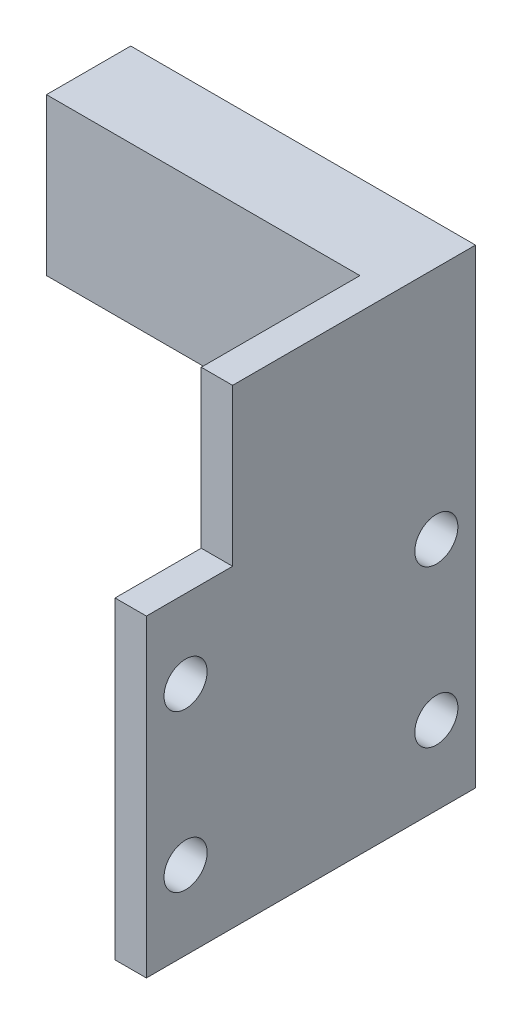
SolidWorks part; units mm, degrees
ref_plane "Front Plane" through (0, 0, 0) normal (0, 0, 1) x (1, 0, 0)
ref_plane "Top Plane" through (0, 0, 0) normal (0, 1, 0) x (1, 0, 0)
ref_plane "Right Plane" through (0, 0, 0) normal (1, 0, 0) x (0, 0, -1)
sketch "Sketch1" plane through (0, 0, 0) normal (1, 0, 0) x (0, 0, -1)
  line L0 (21, 40) -> (21, 0) construction
  line L1 (0, 0) -> (42, 0)
  line L2 (0, 0) -> (0, 40)
  line L3 (0, 40) -> (42, 40)
  line L4 (42, 0) -> (42, 40)
  line L5 (0, 20) -> (42, 20) construction
  circle A0 centre (5, 30) radius 2.75
  circle A2 centre (5, 10) radius 2.75
  circle A3 centre (37, 10) radius 2.75
  circle A4 centre (37, 30) radius 2.75
  dimension "D4" = 5.5
  dimension "D1" = 42
  dimension "D2" = 40
  dimension "D3" = 32
  dimension "D5" = 20
extrude "Boss-Extrude1" add sketch "Sketch1" against normal blind 4
sketch "Sketch3" plane through (0, 40, 0) normal (0, 1, 0) x (1, 0, 0)
  line L11 (0, 42) -> (-44, 42)
  line L12 (-44, 42) -> (-44, 31.25)
  line L13 (-44, 31.25) -> (-4, 31.25)
  line L14 (-4, 42) -> (-4, 0) construction
  line L15 (-4, 31.25) -> (-4, 11)
  line L16 (-4, 11) -> (0, 11)
  line L17 (0, 42) -> (0, 0) construction
  line L18 (0, 11) -> (0, 42)
  line L19 (-4, 0) -> (0, 0) construction
  dimension "D1" = 11
  dimension "D2" = 10.75
  dimension "D3" = 40
extrude "Boss-Extrude2" add sketch "Sketch3" along normal blind 20
